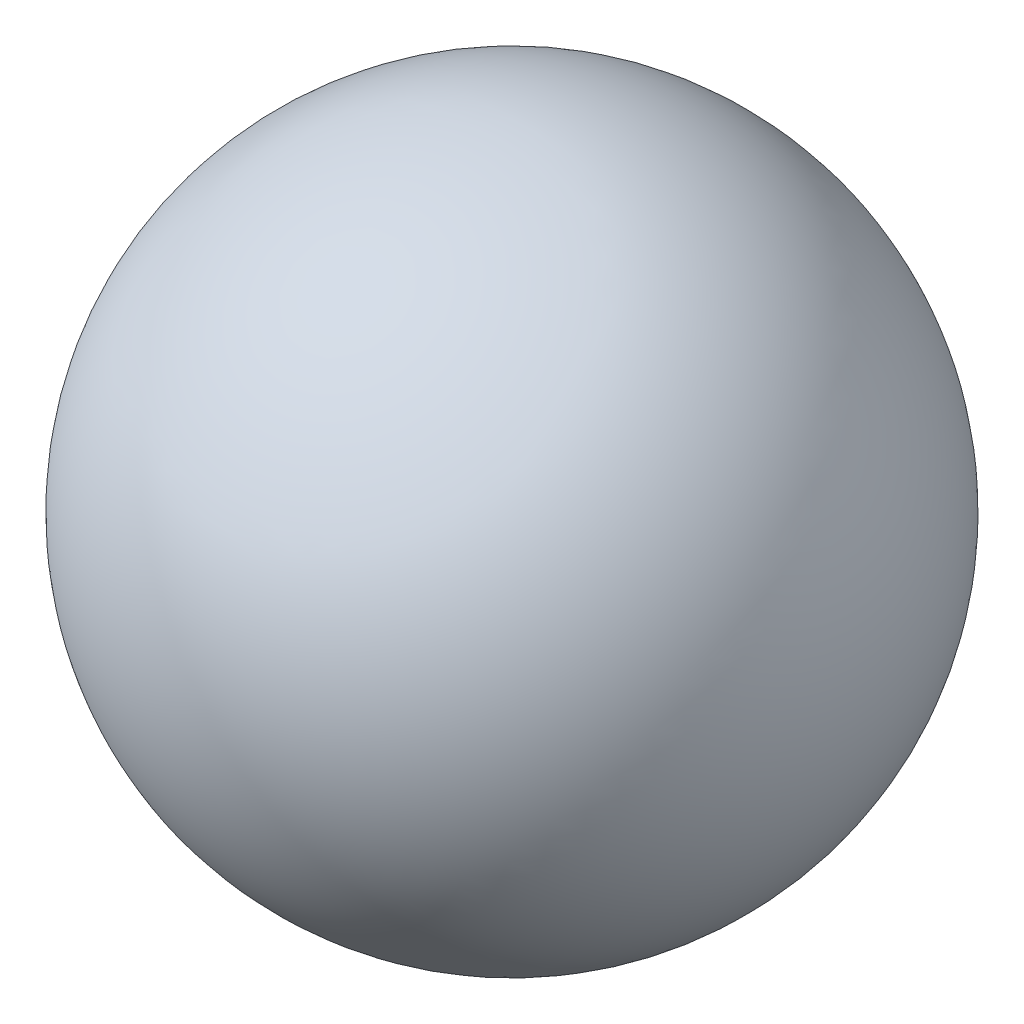
SolidWorks part; units mm, degrees
ref_plane "Front Plane" through (0, 0, 0) normal (0, 0, 1) x (1, 0, 0)
ref_plane "Top Plane" through (0, 0, 0) normal (0, 1, 0) x (1, 0, 0)
ref_plane "Right Plane" through (0, 0, 0) normal (1, 0, 0) x (0, 0, -1)
sketch "Sketch1" plane through (0, 0, 0) normal (0, 1, 0) x (1, 0, 0)
  line L0 (0, 6.35) -> (0, -6.35) construction
  line L1 (0, 6.35) -> (0, -6.35)
  arc A0 (0, 6.35) -> (0, -6.35) centre (0, 0) ccw
  dimension "OD" = 12.7
revolve "Revolve1" add sketch "Sketch1" angle 360 about L0
